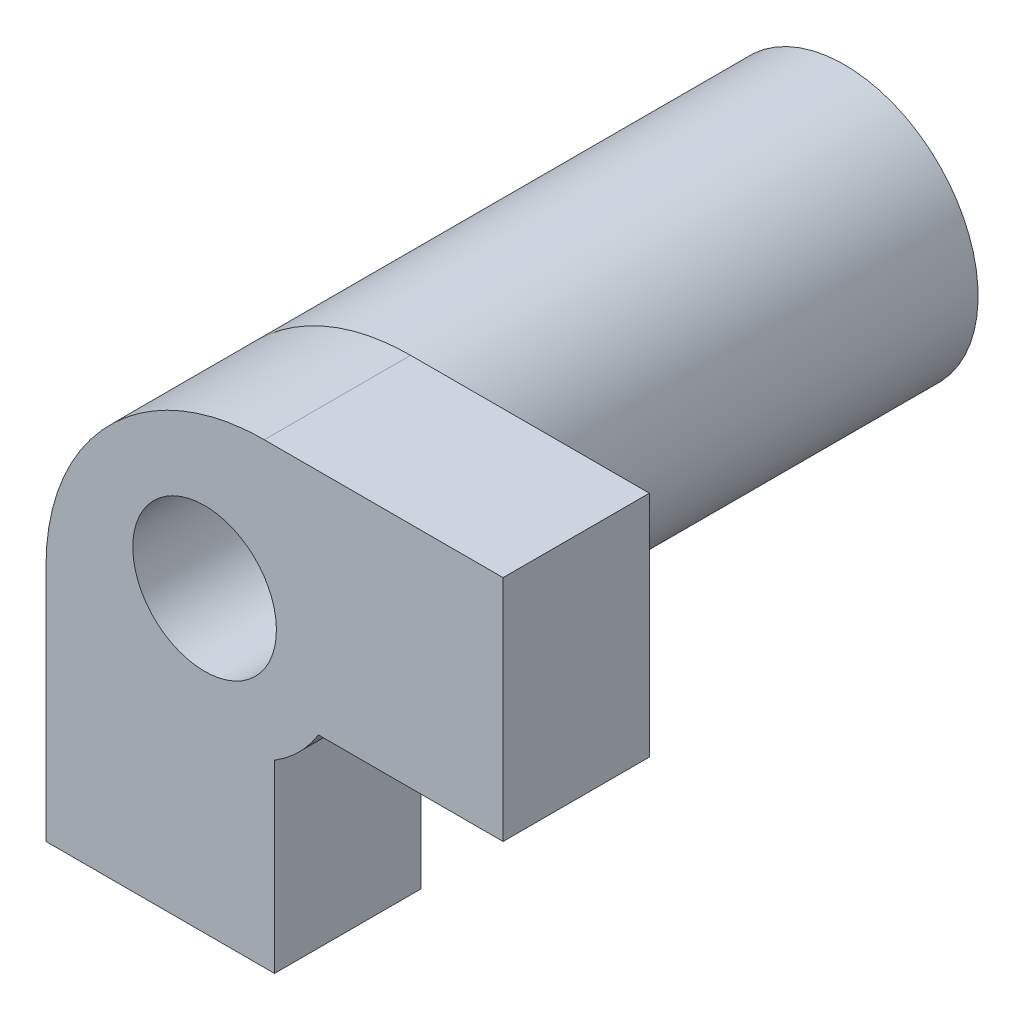
SolidWorks part; units mm, degrees
ref_plane "Alzado" through (0, 0, 0) normal (0, 0, 1) x (1, 0, 0)
ref_plane "Planta" through (0, 0, 0) normal (0, 1, 0) x (1, 0, 0)
ref_plane "Vista lateral" through (0, 0, 0) normal (1, 0, 0) x (0, 0, -1)
sketch "Model" plane through (0, 0, 0) normal (0, 0, 1) x (1, 0, 0)
  line L1 (-3.4528, -6.5302) -> (6.5472, -6.5302)
  line L2 (-3.4528, -6.5302) -> (-3.4528, 3.4698)
  line L3 (-3.4528, 3.4698) -> (6.5472, 3.4698)
  line L4 (6.5472, -6.5302) -> (6.5472, 3.4698)
  ellipse E0 centre (0.0167, 0) end of major axis (0.0167, 1.5712) minor radius 1.5712
  spline S3 degree 3 poles (-3.4528, -1.3064) (-3.4528, 1.3205) (-1.3035, 3.4698) (1.3234, 3.4698) knots 0.777778 0.777778 0.777778 0.777778 1 1 1 1
  point P4 (3.2295, -9.2333)
  point P5 (3.1589, -7.7455)
  dimension "D1" = 0.0167
  dimension "D2" = 1.3234
  dimension "D3" = 1.588
  dimension "D4" = 10
  dimension "D5" = 1.5712
  dimension "D6" = 3.4528
  dimension "D7" = 3.4698
  dimension "D8" = 1.3064
  dimension "D9" = 10
extrude "Saliente-Extruir1" add sketch "Model" along normal blind 3.2 contours S3 L2 L1 L4 L3 E0
sketch "Croquis2" plane through (0, 0, 0) normal (0, 0, -1) x (-1, 0, 0)
  circle A0 centre (-0.0167, 0) radius 2.9227
  circle A1 centre (-0.0167, 0) radius 1.5712 construction
  spline S0 degree 3 poles (3.4528, -1.3064) (3.4528, 1.3205) (1.3035, 3.4698) (-1.3234, 3.4698) knots 0.777778 0.777778 0.777778 0.777778 1 1 1 1 construction
extrude "Saliente-Extruir2" add sketch "Croquis2" along normal blind 10.8
sketch "Croquis3" plane through (0, 0, 0) normal (0, 0, 1) x (1, 0, 0)
  circle A1 centre (0.0167, 0) radius 1.5712
  circle A2 centre (0.0167, 0) radius 1.5712
  dimension "D1" = 0
extrude "Cortar-Extruir1" cut sketch "Croquis3" against normal blind 13.8
sketch "Croquis4" plane through (0, 0, 0) normal (0, 0, -1) x (-1, 0, 0)
  line L0 (-1.3234, 3.4698) -> (-6.5472, 3.4698) construction
  line L1 (-13.4404, -13.3705) -> (-1.5472, -13.3705)
  line L2 (-13.4404, -13.3705) -> (-13.4404, -1.5302)
  line L3 (-13.4404, -1.5302) -> (-2.5069, -1.5302)
  line L4 (-1.5472, -13.3705) -> (-1.5472, -2.49)
  line L5 (3.4528, -6.5302) -> (3.4528, -1.3064) construction
  circle A1 centre (-0.0167, 0) radius 2.9227
  arc A2 (-2.5069, -1.5302) -> (-1.5472, -2.49) centre (-0.0167, 0) ccw
  dimension "D1" = 5
  dimension "D2" = 5
  dimension "D3" = 0
extrude "Cortar-Extruir2" cut sketch "Croquis4" against normal blind 13.8
